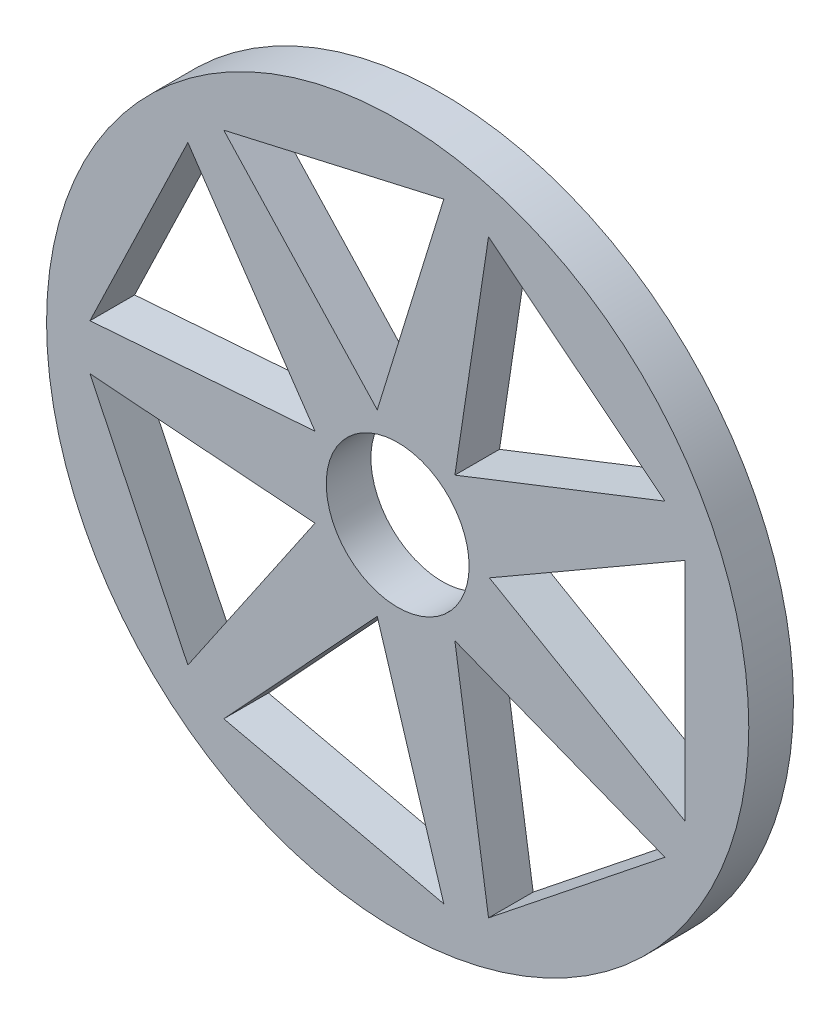
SolidWorks part; units mm, degrees
ref_plane "Front" through (0, 0, 0) normal (0, 0, 1) x (1, 0, 0)
ref_plane "Top" through (0, 0, 0) normal (0, 1, 0) x (1, 0, 0)
ref_plane "Right" through (0, 0, 0) normal (1, 0, 0) x (0, 0, -1)
sketch "Sketch1" plane through (0, 0, 0) normal (0, 0, 1) x (1, 0, 0)
  line L1 (-64.0715, -50.8) -> (-64.0715, 50.8) construction
  circle A0 centre (-9.1425, 0) radius 54.929
  circle A1 centre (-9.1425, 0) radius 2.55 construction
  circle A2 centre (-9.1425, 0) radius 11.176
  dimension "D1" = 22.352
extrude "Boss-Extrude1" add sketch "Sketch1" along normal blind 6.985
sketch "Sketch2" plane through (0, 0, 6.985) normal (0, 0, 1) x (1, 0, 0)
  line L0 (5.2085, 0) -> (35.7865, 17.6542)
  line L1 (35.7865, 17.6542) -> (35.7865, -17.6542)
  line L2 (35.7865, -17.6542) -> (5.2085, 0)
  line L27 (-9.1425, 0) -> (2.0335, 0) construction
  line L28 (2.0335, 0) -> (45.7865, 0) construction
  line L29 (32.6729, -24.1197) -> (5.0677, -46.1341)
  line L30 (-0.1948, -11.2201) -> (32.6729, -24.1197)
  line L31 (5.0677, -46.1341) -> (-0.1948, -11.2201)
  line L32 (-1.9286, -47.731) -> (-36.3517, -39.8741)
  line L33 (-12.3359, -13.9912) -> (-1.9286, -47.731)
  line L34 (-36.3517, -39.8741) -> (-12.3359, -13.9912)
  line L35 (-41.9623, -35.3999) -> (-57.282, -3.5881)
  line L36 (-22.0723, -6.2267) -> (-41.9623, -35.3999)
  line L37 (-57.282, -3.5881) -> (-22.0723, -6.2267)
  line L38 (-57.282, 3.5881) -> (-41.9623, 35.3999)
  line L39 (-22.0723, 6.2267) -> (-57.282, 3.5881)
  line L40 (-41.9623, 35.3999) -> (-22.0723, 6.2267)
  line L41 (-36.3517, 39.8741) -> (-1.9286, 47.731)
  line L42 (-12.3359, 13.9912) -> (-36.3517, 39.8741)
  line L43 (-1.9286, 47.731) -> (-12.3359, 13.9912)
  line L44 (5.0677, 46.1341) -> (32.6729, 24.1197)
  line L45 (-0.1948, 11.2201) -> (5.0677, 46.1341)
  line L46 (32.6729, 24.1197) -> (-0.1948, 11.2201)
  circle A0 centre (-9.1425, 0) radius 11.176 construction
  circle A1 centre (-9.1425, 0) radius 54.929 construction
  circle A2 centre (-9.1425, 0) radius 11.176 construction
  circle A3 centre (-9.1425, 0) radius 54.929 construction
  circle A4 centre (-9.1425, 0) radius 11.176
  circle A5 centre (-9.1425, 0) radius 11.176
  circle A6 centre (-9.1425, 0) radius 11.176
  circle A7 centre (-9.1425, 0) radius 11.176
  circle A8 centre (-9.1425, 0) radius 11.176
  circle A9 centre (-9.1425, 0) radius 11.176
  point P32 (-9.1425, 0)
  point P39 (-9.1425, 0)
  dimension "D1" = 60
  dimension "D2" = 60
  dimension "D3" = 3.175
  dimension "D4" = 10
  dimension "D5" = 7
extrude "Cut-Extrude1" cut sketch "Sketch2" against normal up to surface (6.985 mm away) contours L2 L1 L0 | L31 L29 L30 | L34 L32 L33 | L37 L35 L36 | L40 L38 L39 | L43 L41 L42 | L46 L44 L45 up to face at (45.7865, 0, 0)
